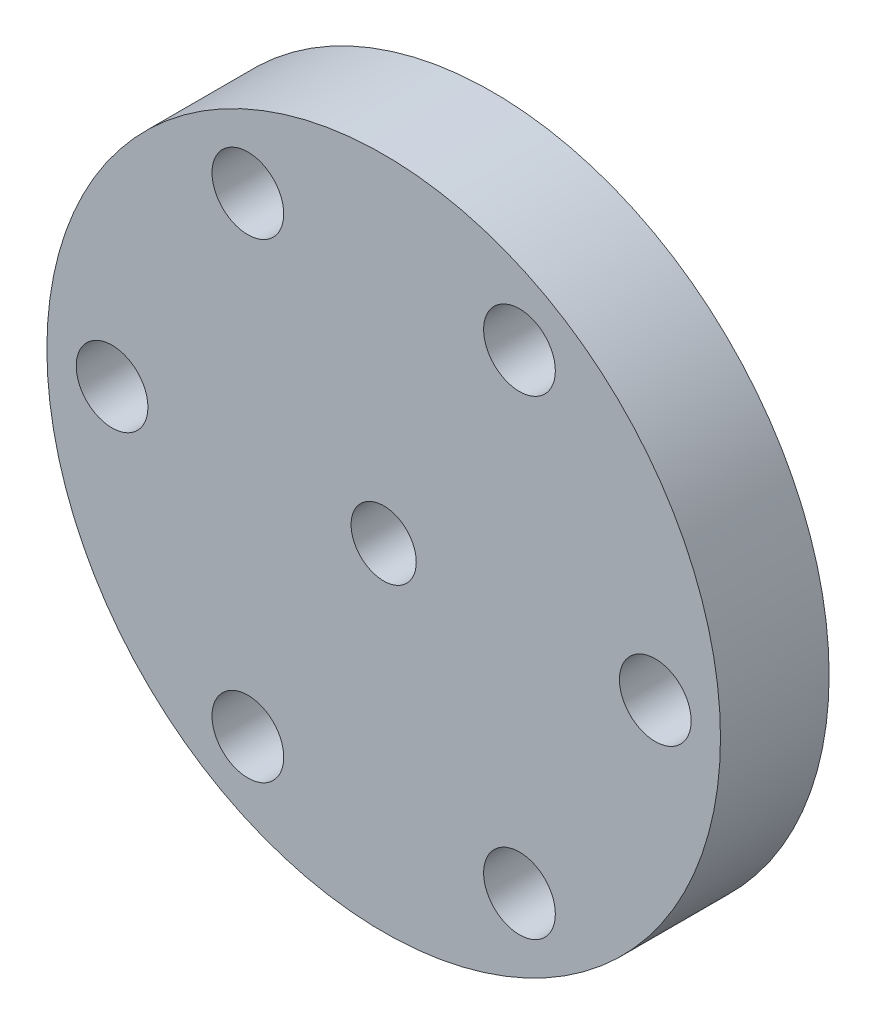
SolidWorks part; units mm, degrees
material "AISI 1020"
ref_plane "Plano frontal" through (0, 0, 0) normal (0, 0, 1) x (1, 0, 0)
ref_plane "Plano superior" through (0, 0, 0) normal (0, 1, 0) x (1, 0, 0)
ref_plane "Plano direito" through (0, 0, 0) normal (1, 0, 0) x (0, 0, -1)
sketch "Esboço2" plane through (0, 0, 0) normal (0, 0, 1) x (1, 0, 0)
  line L1 (-40, -58.6) -> (40, -58.6)
  line L2 (-40, -58.6) -> (-40, 58.6)
  line L3 (-40, 58.6) -> (40, 58.6)
  line L4 (40, -58.6) -> (40, 58.6)
  line L5 (-40, -58.6) -> (40, 58.6) construction
  line L6 (-40, 58.6) -> (40, -58.6) construction
  point P0 (0, 0)
  dimension "D1" = 117.2
  dimension "D2" = 80
extrude "Ressalto-extrusão2" add sketch "Esboço2" along normal mid plane 10
sketch "Esboço3" plane through (0, 0, 5) normal (0, 0, 1) x (1, 0, 0)
  circle A0 centre (0, 0) radius 3
  dimension "D1" = 6
extrude "Corte-extrusão1" cut sketch "Esboço3" against normal through all
cosmetic thread "Representação de rosca11" parameters "D1"=5, "D2"=8
sketch "Esboço4" plane through (0, 0, 5) normal (0, 0, 1) x (1, 0, 0)
  circle A0 centre (12.5, 21.6506) radius 3.3
  dimension "D1" = 6.6
  dimension "D2" = 25
  dimension "D3" = 12.5
extrude "Corte-extrusão2" cut sketch "Esboço4" against normal blind 34.5
cosmetic thread "Representação de rosca7" parameters "D2"=8
pattern_circular "PadrãoCircular1" count 6 over 360 about axis through (0, 0, 0) along (0, 0, 1) of "Corte-extrusão2"
cosmetic thread "Representação de rosca5" parameters "D2"=8
cosmetic thread "Representação de rosca6" parameters "D2"=8
cosmetic thread "Representação de rosca8" parameters "D2"=8
cosmetic thread "Representação de rosca9" parameters "D2"=8
cosmetic thread "Representação de rosca10" parameters "D2"=8
sketch "Esboço6" plane through (0, 0, 5) normal (0, 0, 1) x (1, 0, 0)
  circle A0 centre (0, 0) radius 31
  dimension "D1" = 62
extrude "Corte-extrusão3" [suppressed] cut sketch "Esboço6" against normal blind 10
sketch "Esboço7" plane through (0, -58.6, 0) normal (0, -1, 0) x (1, 0, 0)
  circle A0 centre (0, 0) radius 7.5
  dimension "D1" = 15
extrude "Corte-extrusão4" [suppressed] cut sketch "Esboço7" against normal blind 20
sketch "Esboço10" plane through (0, 58.6, 0) normal (0, 1, 0) x (1, 0, 0)
  line L1 (-40, -5) -> (-40, 5) construction
  line L2 (40, 5) -> (-40, 5) construction
  line L3 (40, -5) -> (-40, -5) construction
  line L4 (40, -5) -> (40, 5) construction
  circle A0 centre (-30, -5) radius 4
  circle A1 centre (30, -5) radius 4
  circle A2 centre (-30, 5) radius 4
  circle A3 centre (30, 5) radius 4
  circle A4 centre (-15, 0) radius 3
  circle A5 centre (15, 0) radius 3
  point P18 (-40, 0)
  dimension "D1" = 8
  dimension "D2" = 8
  dimension "D5" = 10
  dimension "D6" = 10
  dimension "D3" = 8
  dimension "D7" = 6
  dimension "D8" = 10
  dimension "D9" = 10
  dimension "D10" = 6
  dimension "D11" = 25
  dimension "D12" = 10
  dimension "D13" = 10
  dimension "D14" = 25
  dimension "D15" = 10
  dimension "D16" = 8
  dimension "D4" = 10
extrude "Corte-extrusão5" [suppressed] cut sketch "Esboço10" against normal blind 30
cosmetic thread "Representação de rosca1" [suppressed] parameters "D2"=10
cosmetic thread "Representação de rosca2" [suppressed] parameters "D2"=10
cosmetic thread "Representação de rosca3" [suppressed] parameters "D2"=10
cosmetic thread "Representação de rosca4" [suppressed] parameters "D2"=10
sketch "Esboço11" plane through (0, 0, 5) normal (0, 0, 1) x (1, 0, 0)
  line L0 (40, 58.6) -> (-40, 58.6) construction
  line L1 (-10, 58.6) -> (10, 58.6)
  line L2 (-10, 58.6) -> (-10, 51.6)
  line L3 (-10, 51.6) -> (10, 51.6)
  line L4 (10, 58.6) -> (10, 51.6)
  dimension "D1" = 20
  dimension "D2" = 10
  dimension "D3" = 7
extrude "Corte-extrusão6" [suppressed] cut sketch "Esboço11" against normal through all
sketch "Esboço12" plane through (0, 0, 5) normal (0, 0, 1) x (1, 0, 0)
  line L0 (40, -58.6) -> (40, 58.6) construction
  line L1 (-40, -58.6) -> (40, -58.6)
  line L2 (-40, -58.6) -> (-40, -41.4)
  line L3 (-40, -41.4) -> (40, -41.4)
  line L4 (40, -58.6) -> (40, -41.4)
  dimension "D1" = 17.2
extrude "Corte-extrusão7" cut sketch "Esboço12" against normal through all
thread "Rosca1" [suppressed] pitch 1.25 start angle 0, offset 0, length 0, pitch 1.25, diameter 8
ref_plane "Plano1" through (-34, 58.6, -12.225) normal (0, 0, 1) x (-1, 0, 0)
sketch "Perfil da rosca1" plane through (-34, 58.6, -12.225) normal (0, 0, 1) x (-1, 0, 0)
  line L0 (0, 0) -> (0, 1.25) construction
  line L11 (0, 0) -> (0, 1.0937)
  line L12 (0, 1.0937) -> (-0.6766, 0.7031)
  line L13 (-0.6766, 0.7031) -> (-0.6766, 0.3906)
  line L15 (-0.6766, 0.3906) -> (0, 0)
  line L17 (-0.6766, 0.5469) -> (0, 0.5469) construction
  point P2 (0, 0)
  dimension "Pitch" = 1.25
  dimension "Profile_Angle" = 60
  dimension "Profile_Land" = 0.3125
  dimension "Profile_Height" = 0.6766
thread "Rosca2" [suppressed] pitch 1.25 start angle 0, offset 0, length 0, pitch 1.25, diameter 8
ref_plane "Plano2" through (-34, 58.6, 12.225) normal (0, 0, 1) x (-1, 0, 0)
sketch "Perfil da rosca2" plane through (-34, 58.6, 12.225) normal (0, 0, 1) x (-1, 0, 0)
  line L0 (0, 0) -> (0, 1.25) construction
  line L11 (0, 0) -> (0, 1.0937)
  line L12 (0, 1.0937) -> (-0.6766, 0.7031)
  line L13 (-0.6766, 0.7031) -> (-0.6766, 0.3906)
  line L15 (-0.6766, 0.3906) -> (0, 0)
  line L17 (-0.6766, 0.5469) -> (0, 0.5469) construction
  point P2 (0, 0)
  dimension "Pitch" = 1.25
  dimension "Profile_Angle" = 60
  dimension "Profile_Land" = 0.3125
  dimension "Profile_Height" = 0.6766
thread "Rosca3" [suppressed] pitch 1.25 start angle 0, offset 0, length 0, pitch 1.25, diameter 8
ref_plane "Plano3" through (26, 58.6, -12.225) normal (0, 0, 1) x (-1, 0, 0)
sketch "Perfil da rosca3" plane through (26, 58.6, -12.225) normal (0, 0, 1) x (-1, 0, 0)
  line L0 (0, 0) -> (0, 1.25) construction
  line L11 (0, 0) -> (0, 1.0937)
  line L12 (0, 1.0937) -> (-0.6766, 0.7031)
  line L13 (-0.6766, 0.7031) -> (-0.6766, 0.3906)
  line L15 (-0.6766, 0.3906) -> (0, 0)
  line L17 (-0.6766, 0.5469) -> (0, 0.5469) construction
  point P2 (0, 0)
  dimension "Pitch" = 1.25
  dimension "Profile_Angle" = 60
  dimension "Profile_Land" = 0.3125
  dimension "Profile_Height" = 0.6766
thread "Rosca4" [suppressed] pitch 1.25 start angle 0, offset 0, length 0, pitch 1.25, diameter 8
ref_plane "Plano4" through (26, 58.6, 12.225) normal (0, 0, 1) x (-1, 0, 0)
sketch "Perfil da rosca4" plane through (26, 58.6, 12.225) normal (0, 0, 1) x (-1, 0, 0)
  line L0 (0, 0) -> (0, 1.25) construction
  line L11 (0, 0) -> (0, 1.0937)
  line L12 (0, 1.0937) -> (-0.6766, 0.7031)
  line L13 (-0.6766, 0.7031) -> (-0.6766, 0.3906)
  line L15 (-0.6766, 0.3906) -> (0, 0)
  line L17 (-0.6766, 0.5469) -> (0, 0.5469) construction
  point P2 (0, 0)
  dimension "Pitch" = 1.25
  dimension "Profile_Angle" = 60
  dimension "Profile_Land" = 0.3125
  dimension "Profile_Height" = 0.6766
thread "Rosca5" [suppressed] pitch 1.25 start angle 0, offset 0, length 0, pitch 1.25, diameter 6.6
ref_plane "Plano5" through (-15.8, 21.6506, 22.225) normal (0, -1, 0) x (-1, 0, 0)
sketch "Perfil da rosca5" plane through (-15.8, 21.6506, 22.225) normal (0, -1, 0) x (-1, 0, 0)
  line L0 (0, 0) -> (0, 1.25) construction
  line L11 (0, 0) -> (0, 1.0937)
  line L12 (0, 1.0937) -> (-0.6766, 0.7031)
  line L13 (-0.6766, 0.7031) -> (-0.6766, 0.3906)
  line L15 (-0.6766, 0.3906) -> (0, 0)
  line L17 (-0.6766, 0.5469) -> (0, 0.5469) construction
  point P2 (0, 0)
  dimension "Pitch" = 1.25
  dimension "Profile_Angle" = 60
  dimension "Profile_Land" = 0.3125
  dimension "Profile_Height" = 0.6766
thread "Rosca6" [suppressed] pitch 1.25 start angle 0, offset 0, length 0, pitch 1.25, diameter 6.6
ref_plane "Plano6" through (9.2, 21.6506, 22.225) normal (0, -1, 0) x (-1, 0, 0)
sketch "Perfil da rosca6" plane through (9.2, 21.6506, 22.225) normal (0, -1, 0) x (-1, 0, 0)
  line L0 (0, 0) -> (0, 1.25) construction
  line L11 (0, 0) -> (0, 1.0937)
  line L12 (0, 1.0937) -> (-0.6766, 0.7031)
  line L13 (-0.6766, 0.7031) -> (-0.6766, 0.3906)
  line L15 (-0.6766, 0.3906) -> (0, 0)
  line L17 (-0.6766, 0.5469) -> (0, 0.5469) construction
  point P2 (0, 0)
  dimension "Pitch" = 1.25
  dimension "Profile_Angle" = 60
  dimension "Profile_Land" = 0.3125
  dimension "Profile_Height" = 0.6766
thread "Rosca7" [suppressed] pitch 1.25 start angle 0, offset 0, length 0, pitch 1.25, diameter 6.6
ref_plane "Plano7" through (-28.3, 0, 22.225) normal (0, -1, 0) x (-1, 0, 0)
sketch "Perfil da rosca7" plane through (-28.3, 0, 22.225) normal (0, -1, 0) x (-1, 0, 0)
  line L0 (0, 0) -> (0, 1.25) construction
  line L11 (0, 0) -> (0, 1.0937)
  line L12 (0, 1.0937) -> (-0.6766, 0.7031)
  line L13 (-0.6766, 0.7031) -> (-0.6766, 0.3906)
  line L15 (-0.6766, 0.3906) -> (0, 0)
  line L17 (-0.6766, 0.5469) -> (0, 0.5469) construction
  point P2 (0, 0)
  dimension "Pitch" = 1.25
  dimension "Profile_Angle" = 60
  dimension "Profile_Land" = 0.3125
  dimension "Profile_Height" = 0.6766
thread "Rosca8" [suppressed] pitch 1.25 start angle 0, offset 0, length 0, pitch 1.25, diameter 6.6
ref_plane "Plano8" through (-15.8, -21.6506, 22.225) normal (0, -1, 0) x (-1, 0, 0)
sketch "Perfil da rosca8" plane through (-15.8, -21.6506, 22.225) normal (0, -1, 0) x (-1, 0, 0)
  line L0 (0, 0) -> (0, 1.25) construction
  line L11 (0, 0) -> (0, 1.0937)
  line L12 (0, 1.0937) -> (-0.6766, 0.7031)
  line L13 (-0.6766, 0.7031) -> (-0.6766, 0.3906)
  line L15 (-0.6766, 0.3906) -> (0, 0)
  line L17 (-0.6766, 0.5469) -> (0, 0.5469) construction
  point P2 (0, 0)
  dimension "Pitch" = 1.25
  dimension "Profile_Angle" = 60
  dimension "Profile_Land" = 0.3125
  dimension "Profile_Height" = 0.6766
thread "Rosca9" [suppressed] pitch 1.25 start angle 0, offset 0, length 0, pitch 1.25, diameter 6.6
ref_plane "Plano9" through (9.2, -21.6506, 22.225) normal (0, -1, 0) x (-1, 0, 0)
sketch "Perfil da rosca9" plane through (9.2, -21.6506, 22.225) normal (0, -1, 0) x (-1, 0, 0)
  line L0 (0, 0) -> (0, 1.25) construction
  line L11 (0, 0) -> (0, 1.0937)
  line L12 (0, 1.0937) -> (-0.6766, 0.7031)
  line L13 (-0.6766, 0.7031) -> (-0.6766, 0.3906)
  line L15 (-0.6766, 0.3906) -> (0, 0)
  line L17 (-0.6766, 0.5469) -> (0, 0.5469) construction
  point P2 (0, 0)
  dimension "Pitch" = 1.25
  dimension "Profile_Angle" = 60
  dimension "Profile_Land" = 0.3125
  dimension "Profile_Height" = 0.6766
thread "Rosca10" [suppressed] pitch 1.25 start angle 0, offset 0, length 0, pitch 1.25, diameter 6.6
ref_plane "Plano10" through (21.7, 0, 22.225) normal (0, -1, 0) x (-1, 0, 0)
sketch "Perfil da rosca10" plane through (21.7, 0, 22.225) normal (0, -1, 0) x (-1, 0, 0)
  line L0 (0, 0) -> (0, 1.25) construction
  line L11 (0, 0) -> (0, 1.0937)
  line L12 (0, 1.0937) -> (-0.6766, 0.7031)
  line L13 (-0.6766, 0.7031) -> (-0.6766, 0.3906)
  line L15 (-0.6766, 0.3906) -> (0, 0)
  line L17 (-0.6766, 0.5469) -> (0, 0.5469) construction
  point P2 (0, 0)
  dimension "Pitch" = 1.25
  dimension "Profile_Angle" = 60
  dimension "Profile_Land" = 0.3125
  dimension "Profile_Height" = 0.6766
chamfer "Chanfro1" [suppressed] distance 20 angle 45
sketch "Esboço13" plane through (0, 0, 5) normal (0, 0, 1) x (1, 0, 0)
  line L1 (-40, 58.6) -> (40, 58.6)
  line L2 (-40, 58.6) -> (-40, -41.4)
  line L3 (-40, -41.4) -> (40, -41.4)
  line L4 (40, 58.6) -> (40, -41.4)
  circle A0 centre (0, 0) radius 31
  dimension "D1" = 62
extrude "Corte-extrusão8" cut sketch "Esboço13" against normal through all
